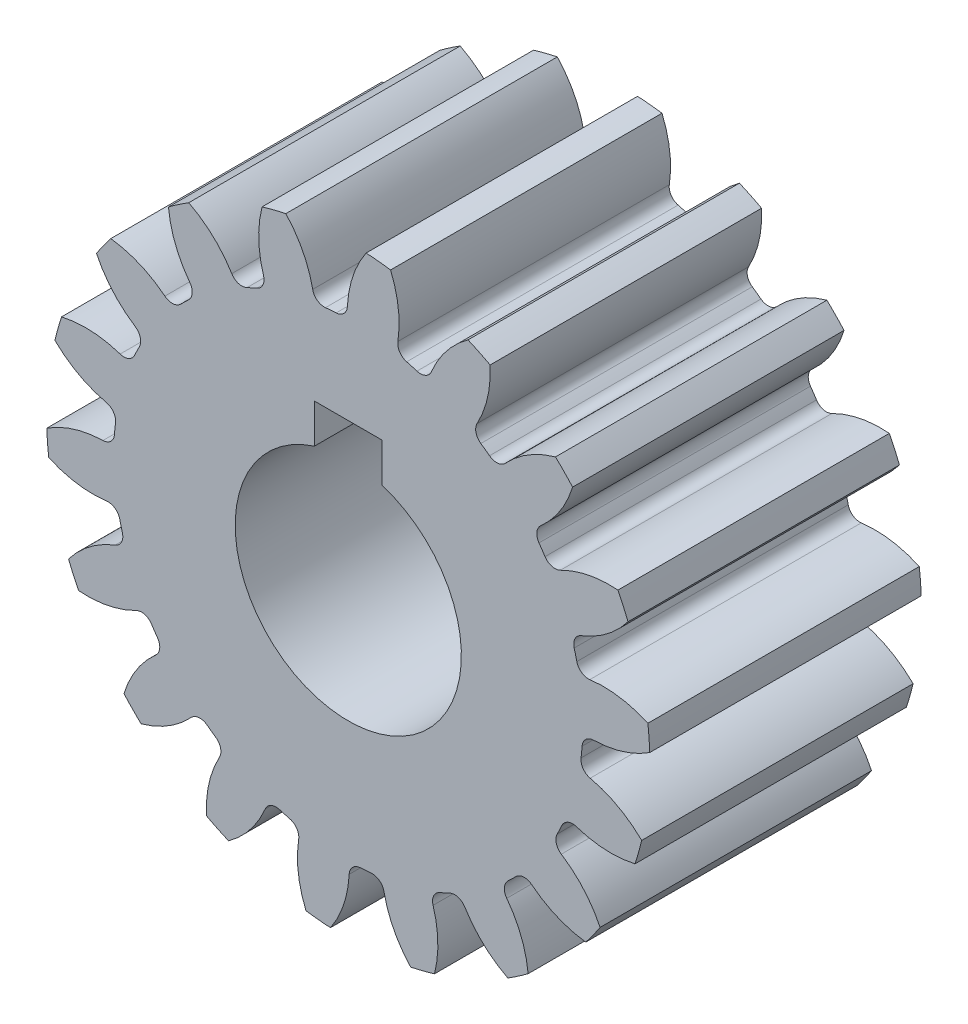
SolidWorks part; units mm, degrees
material "Plain Carbon Steel"
ref_plane "Front" through (0, 0, 0) normal (0, 0, 1) x (1, 0, 0)
ref_plane "Top" through (0, 0, 0) normal (0, 1, 0) x (1, 0, 0)
ref_plane "Right" through (0, 0, 0) normal (1, 0, 0) x (0, 0, -1)
sketch "Sketch3" plane through (0, 0, 0) normal (0, 0, 1) x (1, 0, 0)
  circle A0 centre (0, 0) radius 21.1667
  dimension "od" = 42.3333
extrude "gearBody" add sketch "Sketch3" along normal blind 19.05
sketch "Sketch2" plane through (0, 0, 0) normal (0, 0, 1) x (1, 0, 0)
  line L0 (0, 0) -> (17.0393, 7.0579) construction
  line L1 (22.2652, -7.3645) -> (0, 0) construction
  line L2 (0, 0) -> (36.3143, 0) construction
  line L3 (19.0486, -0.229) -> (18.7151, -3.5564) construction
  line L5 (18.8819, -1.8927) -> (0, 0) construction
  line L7 (0, 0) -> (18.4432, 0) construction
  arc A0 (18.4395, -0.3701) -> (18.1461, -3.2972) centre (0, 0) ccw construction
  arc A1 (21.1545, 0.7174) -> (20.5912, -4.902) centre (0, 0) ccw construction
  arc A2 (19.0486, -0.229) -> (18.7151, -3.5564) centre (0, 0) ccw construction
  arc A3 (16.3353, -2.016) -> (16.4104, -1.2664) centre (0, 0) ccw
  arc A4 (22.2652, -7.3645) -> (16.9763, -2.929) centre (15.2994, -10.2995) ccw
  arc A5 (22.2652, -7.3645) -> (23.2839, 2.7987) centre (0, 0) ccw
  arc A6 (23.2839, 2.7987) -> (17.2199, -0.4988) centre (17.0393, 7.0579) cw
  arc A7 (16.4104, -1.2664) -> (17.2199, -0.4988) centre (17.2398, -1.3304) cw
  arc A8 (16.9763, -2.929) -> (16.3353, -2.016) centre (17.1609, -2.1179) cw
  point P6 (23.2839, 2.7987)
  point P22 (22.2652, -7.3645)
  dimension "baseDia" = 36.8864
  dimension "od" = 42.3333
  dimension "pd" = 38.1
  dimension "rd" = 32.9184
  dimension "rFillet" = 0.8318
  dimension "pointX" = 23.2839
  dimension "pointY" = 2.7987
  dimension "CTT" = 3.3274
  dimension "flankCenterAngle" = 22.5
extrude "toothCut" cut sketch "Sketch2" along normal through all
pattern_circular "CirPattern1" count 18 over 360 about axis through (0, 0, 0) along (0, 0, 1) of "toothCut"
sketch "hub1Dia" plane through (0, 0, 0) normal (0, 0, -1) x (-1, 0, 0)
  circle A0 centre (0, 0) radius 12.7
  dimension "hub1Dia" = 25.4
sketch "hub2Dia" plane through (0, 0, 19.05) normal (0, 0, 1) x (1, 0, 0)
  circle A0 centre (0, 0) radius 12.7
  dimension "hub2dia" = 25.4
sketch "boreDia" plane through (0, 0, 0) normal (0, 0, 1) x (1, 0, 0)
  circle A0 centre (0, 0) radius 7.9375
  dimension "boreDia" = 15.875
extrude "bore" cut sketch "boreDia" against normal mid plane 25400
sketch "Sketch4" plane through (0, 0, 0) normal (0, 0, -1) x (-1, 0, 0)
  line L0 (0, 7.9375) -> (0, 10.3187) construction
  line L1 (0, 10.3187) -> (2.3813, 10.3187)
  line L2 (2.3813, 10.3187) -> (2.3813, 7.5719)
  line L3 (0, 10.3187) -> (-2.3813, 10.3187)
  line L4 (-2.3813, 10.3187) -> (-2.3812, 7.5719)
  circle A0 centre (0, 0) radius 7.9375 construction
  arc A1 (2.3813, 7.5719) -> (-2.3812, 7.5719) centre (0, 0) ccw
  dimension "D1" = 2.3813
  dimension "D2" = 2.3813
  dimension "D3" = 2.3813
extrude "Cut-Extrude1" cut sketch "Sketch4" against normal through all
